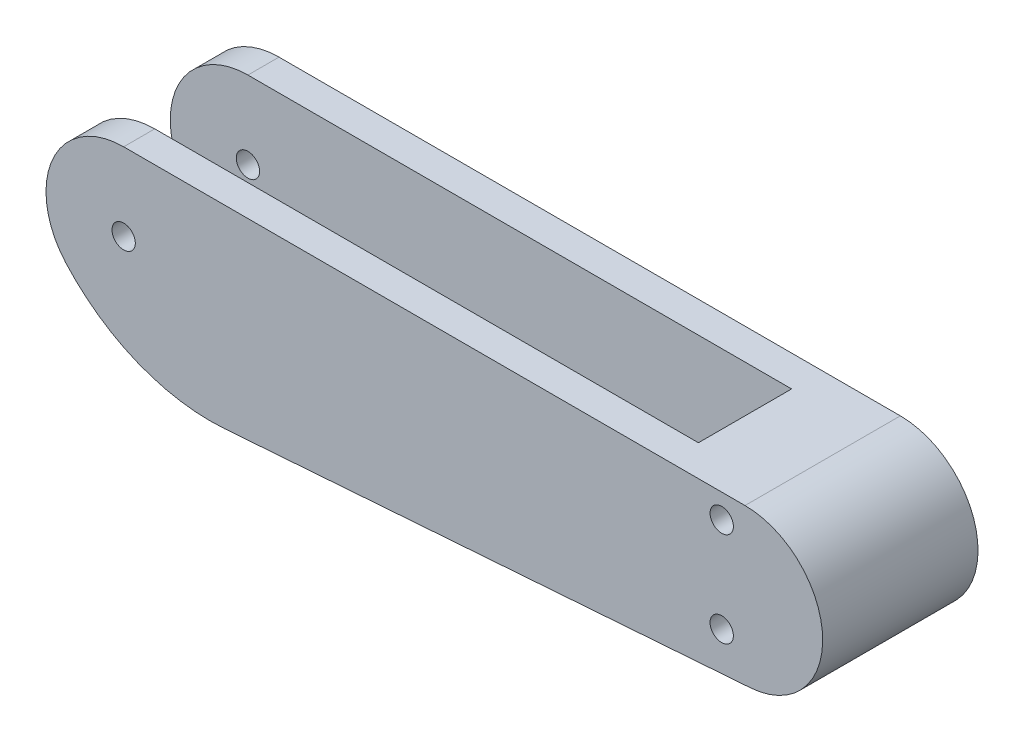
SolidWorks part; units mm, degrees
ref_plane "Front Plane" through (0, 0, 0) normal (0, 0, 1) x (1, 0, 0)
ref_plane "Top Plane" through (0, 0, 0) normal (0, 1, 0) x (1, 0, 0)
ref_plane "Right Plane" through (0, 0, 0) normal (1, 0, 0) x (0, 0, -1)
sketch "Sketch1" plane through (0, 0, 0) normal (0, 0, 1) x (1, 0, 0)
  line L0 (43.628, 10) -> (0, 10)
  line L1 (13.0064, -14.9332) -> (80.7304, -9.9733)
  line L2 (80, 10) -> (43.628, 10)
  arc A0 (-7.4536, -6.6667) -> (13.0064, -14.9332) centre (11.1803, 10) ccw
  arc A1 (80.7304, -9.9733) -> (80, 10) centre (80, 0) ccw
  arc A2 (0, 10) -> (-7.4536, -6.6667) centre (0, 0) ccw
  circle A4 centre (77, -5.283) radius 1.5
  circle A5 centre (77, 6.9049) radius 1.5
  circle A6 centre (0, 0) radius 1.5
  dimension "D2" = 10
  dimension "D4" = 10
  dimension "D3" = 25
  dimension "D5" = 3
  dimension "D1" = 80
  dimension "D6" = 3
extrude "Boss-Extrude1" add sketch "Sketch1" along normal mid plane 20
sketch "Sketch2" plane through (0, 0, 0) normal (0, 1, 0) x (1, 0, 0)
  line L1 (-70, 6) -> (70, 6)
  line L2 (-70, 6) -> (-70, -6)
  line L3 (-70, -6) -> (70, -6)
  line L4 (70, 6) -> (70, -6)
  line L5 (-70, 6) -> (70, -6) construction
  line L6 (-70, -6) -> (70, 6) construction
  line L7 (0, -10) -> (0, 10) construction
  point P0 (0, 0)
  dimension "D1" = 12
  dimension "D2" = 70
extrude "Cut-Extrude1" cut sketch "Sketch2" against normal through all both and the other way through all contours L1 L4 L3 L2
